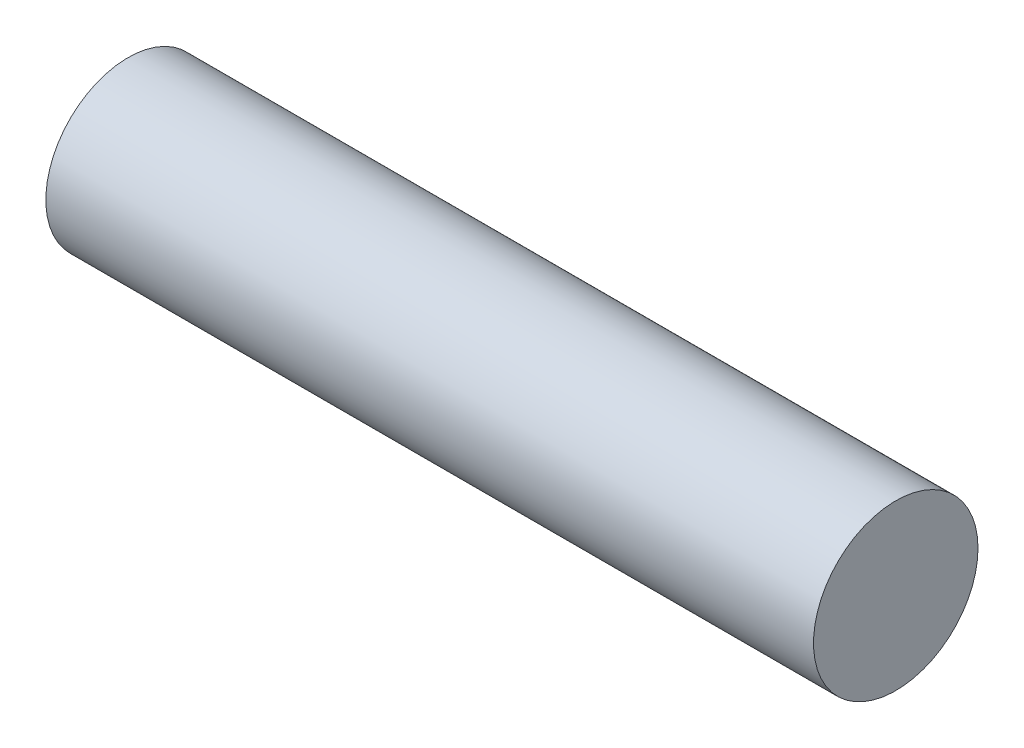
SolidWorks part; units mm, degrees
ref_plane "Front Plane" through (0, 0, 0) normal (0, 0, 1) x (1, 0, 0)
ref_plane "Top Plane" through (0, 0, 0) normal (0, 1, 0) x (1, 0, 0)
ref_plane "Right Plane" through (0, 0, 0) normal (1, 0, 0) x (0, 0, -1)
sketch "Sketch1" plane through (0, 0, 0) normal (1, 0, 0) x (0, 0, -1)
  circle A0 centre (0, 0) radius 7.5
  dimension "D1" = 15
extrude "Boss-Extrude1" add sketch "Sketch1" along normal mid plane 70
